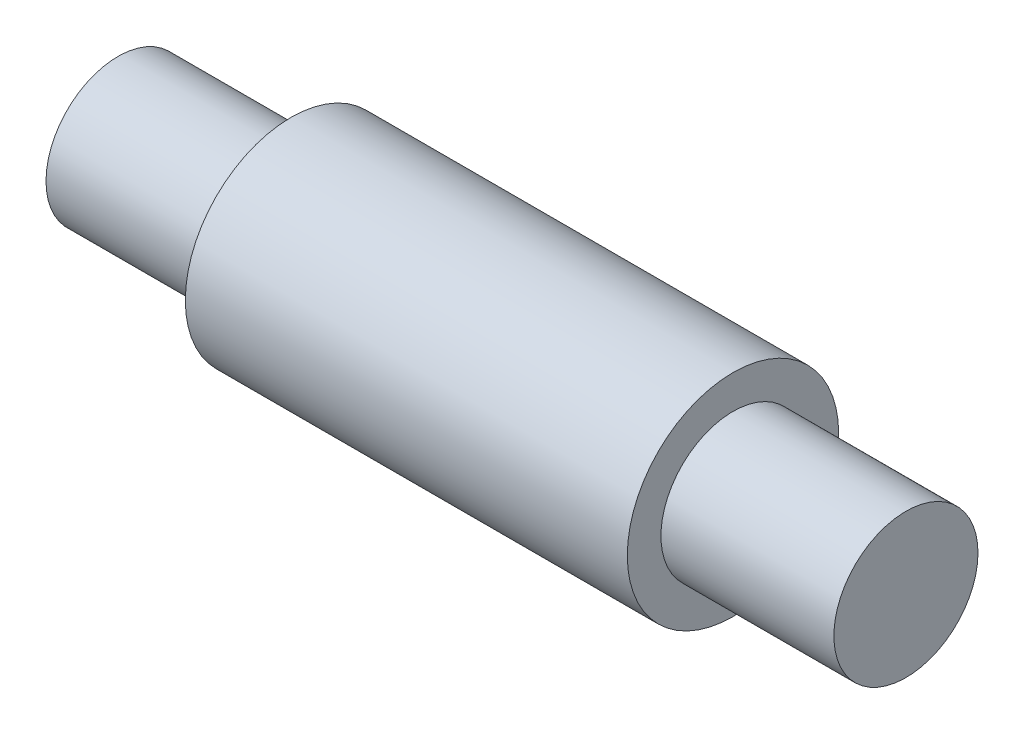
SolidWorks part; units mm, degrees
ref_plane "Front Plane" through (0, 0, 0) normal (0, 0, 1) x (1, 0, 0)
ref_plane "Top Plane" through (0, 0, 0) normal (0, 1, 0) x (1, 0, 0)
ref_plane "Right Plane" through (0, 0, 0) normal (1, 0, 0) x (0, 0, -1)
sketch "Sketch1" plane through (0, 0, 0) normal (1, 0, 0) x (0, 0, -1)
  circle A0 centre (0, 0) radius 11
  dimension "D1" = 22
extrude "Boss-Extrude1" add sketch "Sketch1" along normal blind 46
sketch "Sketch2" plane through (46, 0, 0) normal (1, 0, 0) x (0, 0, -1)
  circle A0 centre (0, 0) radius 7.5
  dimension "D1" = 15
extrude "Boss-Extrude2" add sketch "Sketch2" along normal blind 18
sketch "Sketch3" plane through (0, 0, 0) normal (-1, 0, 0) x (0, 0, 1)
  circle A0 centre (0, 0) radius 7.5
  dimension "D1" = 15
extrude "Boss-Extrude3" add sketch "Sketch3" along normal blind 18
